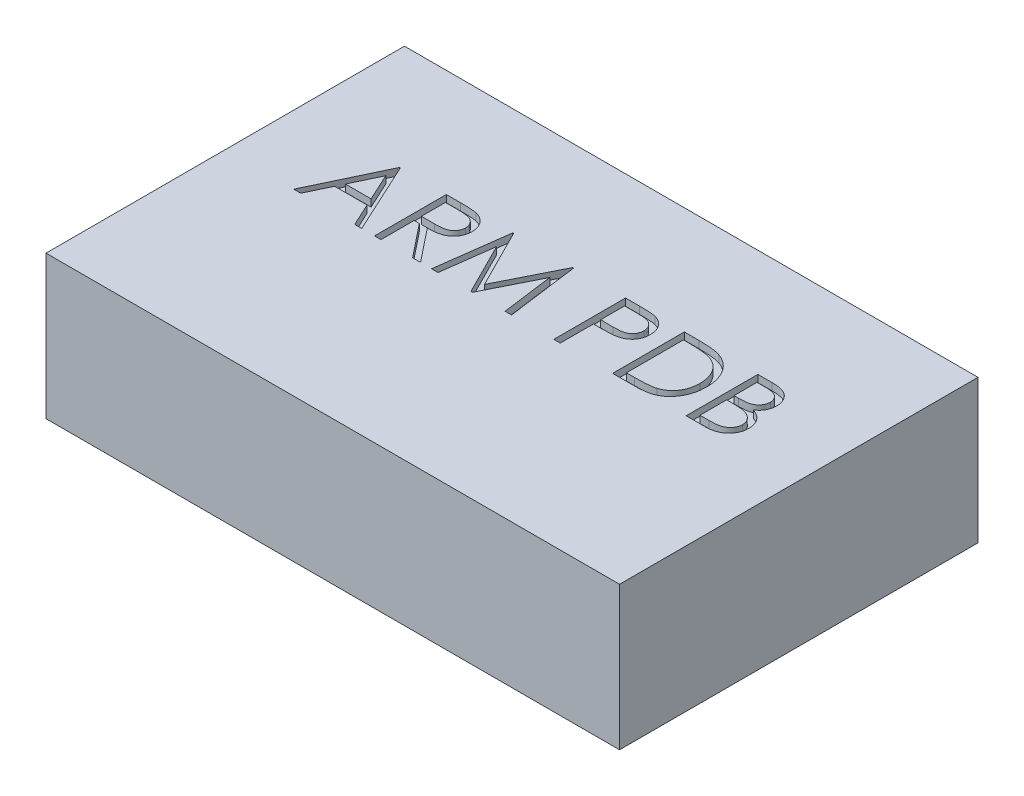
SolidWorks part; units mm, degrees
ref_plane "Front Plane" through (0, 0, 0) normal (0, 0, 1) x (1, 0, 0)
ref_plane "Top Plane" through (0, 0, 0) normal (0, 1, 0) x (1, 0, 0)
ref_plane "Right Plane" through (0, 0, 0) normal (1, 0, 0) x (0, 0, -1)
sketch "Sketch1" plane through (0, 0, 0) normal (0, 1, 0) x (1, 0, 0)
  line L1 (0, 0) -> (80, 0)
  line L2 (0, 0) -> (0, 50)
  line L3 (0, 50) -> (80, 50)
  line L4 (80, 0) -> (80, 50)
  dimension "D1" = 50
  dimension "D2" = 80
extrude "Boss-Extrude1" add sketch "Sketch1" along normal blind 20
sketch "Sketch2" plane through (0, 20, 0) normal (0, 1, 0) x (1, 0, 0)
  line L0 (0, 25) -> (80, 25) construction
  line L1 (0, 50) -> (0, 0) construction
  line L2 (80, 0) -> (80, 50) construction
  text T0 "ARM PDB" font "Century Gothic" height 10
extrude "Cut-Extrude1" cut sketch "Sketch2" against normal blind 1
